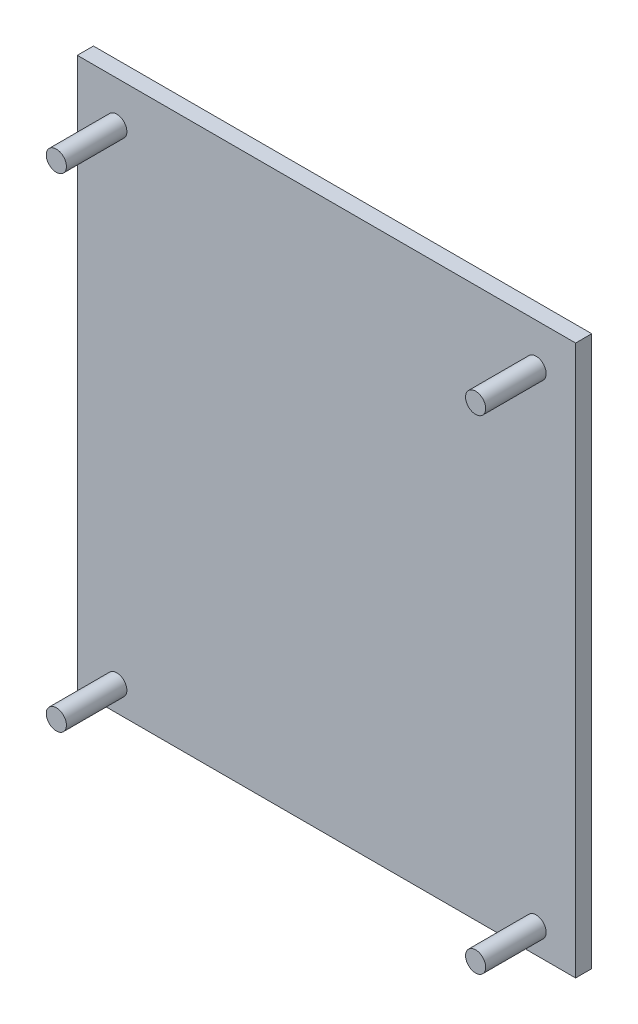
SolidWorks part; units mm, degrees
ref_plane "Front Plane" through (0, 0, 0) normal (0, 0, 1) x (1, 0, 0)
ref_plane "Top Plane" through (0, 0, 0) normal (0, 1, 0) x (1, 0, 0)
ref_plane "Right Plane" through (0, 0, 0) normal (1, 0, 0) x (0, 0, -1)
sketch "Sketch1" plane through (0, 0, 0) normal (0, 0, 1) x (1, 0, 0)
  line L1 (0, 86.614) -> (78.486, 86.614)
  line L2 (0, 86.614) -> (0, 0)
  line L3 (0, 0) -> (78.486, 0)
  line L4 (78.486, 86.614) -> (78.486, 0)
  dimension "D4" = 78.486
  dimension "D5" = 86.614
extrude "Boss-Extrude1" add sketch "Sketch1" along normal blind 2.54
sketch "Sketch2" plane through (0, 0, 2.54) normal (0, 0, 1) x (1, 0, 0)
  line L0 (6.223, 80.1116) -> (72.263, 80.1116) construction
  line L5 (72.263, 80.1116) -> (72.263, 3.9116) construction
  line L6 (72.263, 3.9116) -> (6.223, 3.9116) construction
  line L7 (6.223, 3.9116) -> (6.223, 80.1116) construction
  line L8 (39.243, 86.614) -> (39.243, 0) construction
  line L9 (6.223, 42.0116) -> (72.263, 42.0116) construction
  line L10 (0, 0) -> (78.486, 0) construction
  line L11 (78.486, 86.614) -> (0, 86.614) construction
  line L12 (78.486, 0) -> (78.486, 86.614) construction
  circle A0 centre (6.223, 80.1116) radius 1.5875
  circle A1 centre (72.263, 80.1116) radius 1.5875
  circle A2 centre (72.263, 3.9116) radius 1.5875
  circle A3 centre (6.223, 3.9116) radius 1.5875
  point P18 (39.243, 42.0116)
  point P22 (39.243, 43.307)
  dimension "D3" = 3.175
  dimension "D1" = 76.2
  dimension "D2" = 66.04
  dimension "D4" = 1.2954
extrude "Boss-Extrude2" add sketch "Sketch2" along normal blind 9.525
